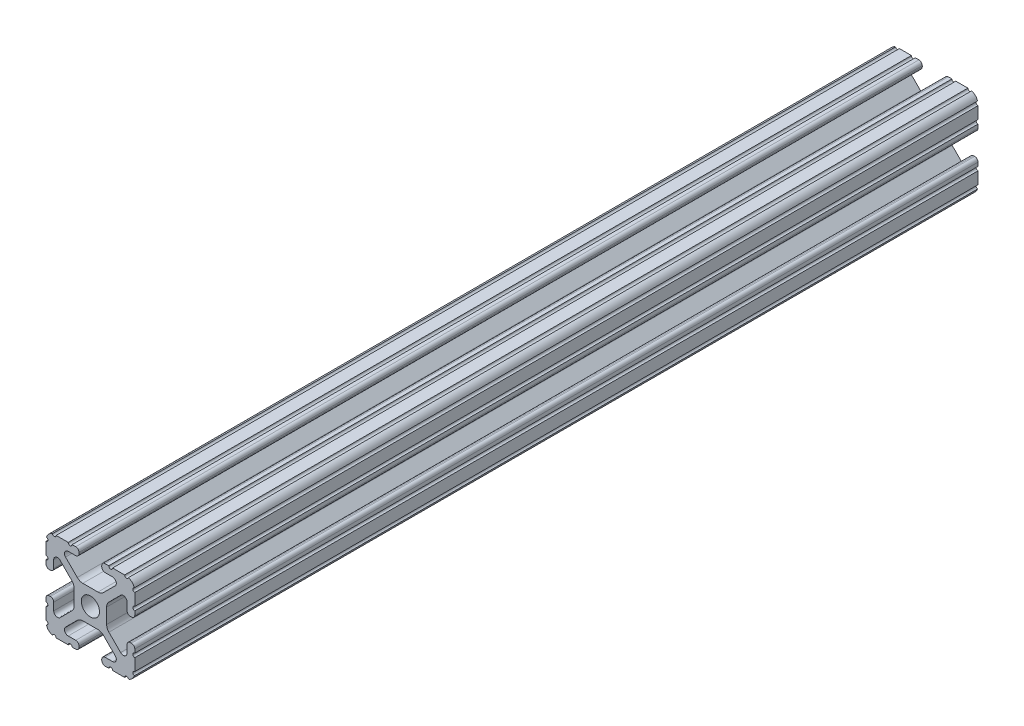
SolidWorks part; units mm, degrees
ref_plane "Front Plane" through (0, 0, 0) normal (0, 0, 1) x (1, 0, 0)
ref_plane "Top Plane" through (0, 0, 0) normal (0, 1, 0) x (1, 0, 0)
ref_plane "Right Plane" through (0, 0, 0) normal (1, 0, 0) x (0, 0, -1)
sketch "Sketch2" plane through (0, 0, 0) normal (0, 0, 1) x (1, 0, 0)
  line L0 (0, 12.7) -> (0, -12.7) construction
  line L1 (-12.7, 0) -> (12.7, 0) construction
  line L2 (3.2512, -12.7) -> (12.7, -12.7)
  line L3 (12.7, -12.7) -> (12.7, -3.2512)
  line L4 (3.2512, -12.7) -> (3.2512, -10.4902)
  line L5 (3.2512, -10.4902) -> (8.9276, -10.4902)
  line L6 (8.9276, -10.4902) -> (3.0856, -4.6482)
  line L7 (0, 0) -> (12.7, -12.7) construction
  line L8 (12.7, -3.2512) -> (10.4902, -3.2512)
  line L9 (10.4902, -3.2512) -> (10.4902, -8.9276)
  line L10 (10.4902, -8.9276) -> (4.6482, -3.0856)
  circle A0 centre (0, 0) radius 2.6035
  arc A1 (6.3485, -10.4902) -> (7.1039, -8.6665) centre (6.3485, -9.4219) ccw construction
  point P8 (0, -4.6482)
  dimension "Center Hole Diameter" = 5.207
  dimension "Rail Height" = 25.4
  dimension "Rail Width" = 25.4
  dimension "T-Slot Width" = 6.5024
  dimension "Slot Inner Width" = 14.8336
  dimension "Thickness" = 2.2098
  dimension "Slot Depth" = 5.842
  dimension "D1" = 2.2098
sketch "Sketch3" plane through (0, 0, 0) normal (1, 0, 0) x (0, 0, -1)
  line L0 (-120.65, -12.7) -> (120.65, -12.7) construction
  line L1 (-95.25, 0) -> (95.25, 0) construction
  dimension "Length" = 241.3
  dimension "D1" = 25.4
sketch "Sketch4" plane through (0, 0, 0) normal (0, 0, 1) x (1, 0, 0)
  line L0 (4.1904, -12.7) -> (10.1173, -12.7)
  line L1 (3.2512, -12.7) -> (12.7, -12.7) construction
  line L2 (3.2512, -12.7) -> (3.2512, -10.4902) construction
  line L3 (3.2512, -10.4902) -> (8.9276, -10.4902) construction
  line L4 (3.2512, -11.4294) -> (3.2512, -11.7608)
  line L5 (4.1904, -10.4902) -> (6.3485, -10.4902)
  line L6 (0, -4.6482) -> (2.164, -4.6482)
  line L7 (8.9276, -10.4902) -> (3.0856, -4.6482) construction
  line L8 (3.7373, -5.2999) -> (7.1039, -8.6665)
  line L9 (12.7, -12.7) -> (12.7, -3.2512) construction
  line L10 (10.4902, -8.9276) -> (4.6482, -3.0856) construction
  line L11 (10.4902, -3.2512) -> (10.4902, -8.9276) construction
  line L12 (10.4902, -6.3485) -> (10.4902, -4.1904)
  line L13 (12.7, -3.2512) -> (10.4902, -3.2512) construction
  line L14 (11.4294, -3.2512) -> (11.7608, -3.2512)
  line L15 (12.7, -4.1904) -> (12.7, -10.1173)
  line L16 (8.6665, -7.1039) -> (5.2999, -3.7373)
  line L17 (4.6482, 0) -> (4.6482, -2.164)
  line L18 (-12.7, 0) -> (12.7, 0) construction
  line L19 (0, -4.6482) -> (0, -2.6035)
  line L20 (0, 12.7) -> (0, -12.7) construction
  line L21 (4.6482, 0) -> (2.6035, 0)
  arc A0 (3.2512, -11.7608) -> (4.1904, -12.7) centre (4.1904, -11.7608) ccw
  arc A2 (3.2512, -11.4294) -> (4.1904, -10.4902) centre (4.1904, -11.4294) cw
  arc A3 (6.3485, -10.4902) -> (7.1039, -8.6665) centre (6.3485, -9.4219) ccw
  arc A4 (2.164, -4.6482) -> (3.7373, -5.2999) centre (2.164, -6.8732) cw
  arc A5 (10.1173, -12.7) -> (12.7, -10.1173) centre (10.1173, -10.1173) ccw
  arc A6 (8.6665, -7.1039) -> (10.4902, -6.3485) centre (9.4219, -6.3485) ccw
  arc A7 (10.4902, -4.1904) -> (11.4294, -3.2512) centre (11.4294, -4.1904) cw
  arc A8 (11.7608, -3.2512) -> (12.7, -4.1904) centre (11.7608, -4.1904) cw
  arc A9 (5.2999, -3.7373) -> (4.6482, -2.164) centre (6.8732, -2.164) cw
  circle A10 centre (0, 0) radius 2.6035 construction
  arc A11 (0, -2.6035) -> (2.6035, 0) centre (0, 0) ccw
  dimension "D1" = 2.5827
  dimension "D2" = 2.225
  dimension "D3" = 0.9392
extrude "Boss-Extrude1" add sketch "Sketch4" along normal mid plane 241.3
sketch "Sketch5" plane through (0, 0, 0) normal (0, 0, 1) x (1, 0, 0)
  line L0 (3.2512, -12.7) -> (12.7, -12.7) construction
  line L1 (4.1904, -10.4902) -> (6.3485, -10.4902) construction
  line L3 (0, 0) -> (12.7, -12.7) construction
  line L4 (6.3485, -10.4902) -> (6.3485, -12.7) construction
  line L5 (8.9276, -10.4902) -> (3.0856, -4.6482) construction
  circle A0 centre (10.3562, -12.7) radius 0.5524
  circle A1 centre (5.796, -12.7) radius 0.5524
  circle A2 centre (12.7, -10.3562) radius 0.5524
  circle A3 centre (12.7, -5.796) radius 0.5524
  point P10 (5.2694, -10.4902)
  point P12 (9.4219, -6.3485)
  dimension "D1" = 1.1049
extrude "Cut-Extrude1" cut sketch "Sketch5" against normal through all both and the other way through all
mirror "Mirror1" about plane through (0, 0, 0) normal (1, 0, 0) of bodies 137 134
mirror "Mirror2" about plane through (0, 0, 0) normal (0, 1, 0) of bodies 135
equation "\"D1@Boss-Extrude1\"=\"Length@Sketch3\""
equation "\"D1@Sketch2\"=\"Thickness@Sketch2\""
equation "\"D2@Sketch4\"=\"Slot Inner Width@Sketch2\"*0.15"
equation "\"D1@Sketch4\"=\"D3@Sketch4\"*2.75"
equation "\"D3@Sketch4\"=\"Thickness@Sketch2\"*0.425"
equation "\"D1@Sketch5\"=\"Thickness@Sketch2\"*0.5"
